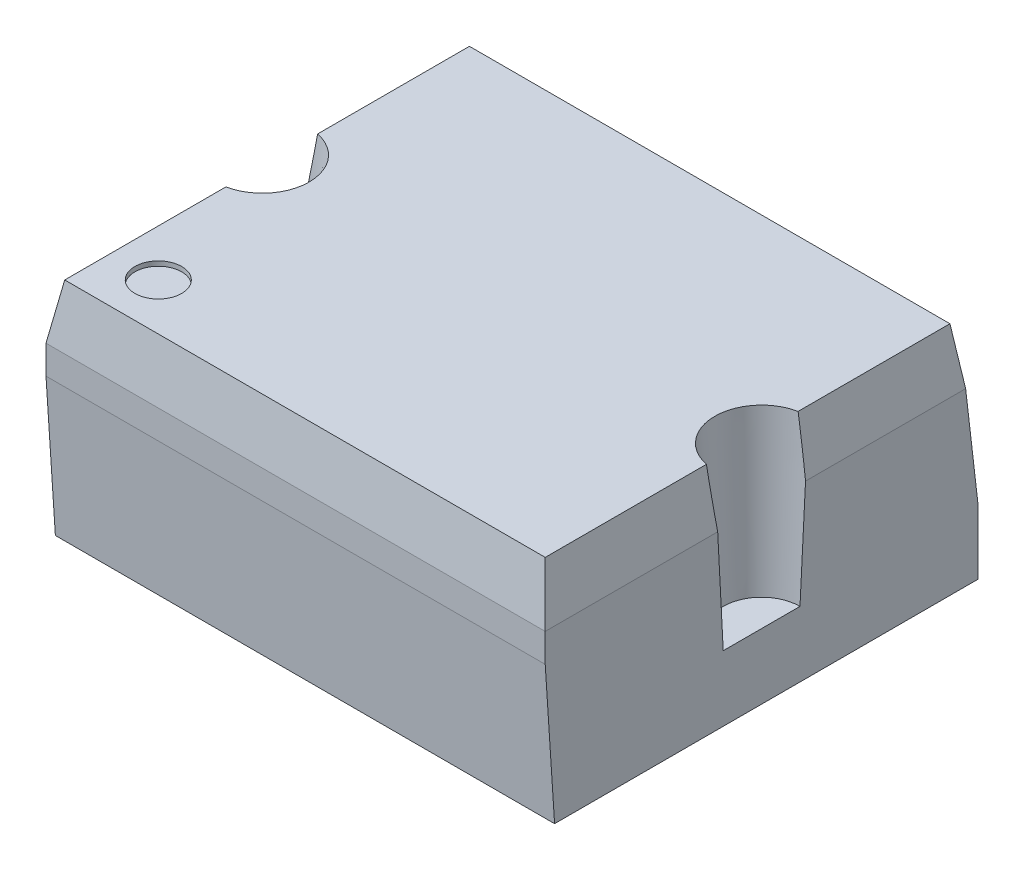
SolidWorks part; units mm, degrees
ref_plane "Front Plane" through (0, 0, 0) normal (0, 0, 1) x (1, 0, 0)
ref_plane "Top Plane" through (0, 0, 0) normal (0, 1, 0) x (1, 0, 0)
ref_plane "Right Plane" through (0, 0, 0) normal (1, 0, 0) x (0, 0, -1)
sketch "Sketch1" plane through (0, 0, 0) normal (0, 1, 0) x (1, 0, 0)
  line L1 (-5.335, -4.625) -> (5.335, -4.625)
  line L2 (-5.335, -4.625) -> (-5.335, 4.625)
  line L3 (-5.335, 4.625) -> (5.335, 4.625)
  line L4 (5.335, -4.625) -> (5.335, 4.625)
  line L5 (-5.335, -4.625) -> (5.335, 4.625) construction
  line L6 (-5.335, 4.625) -> (5.335, -4.625) construction
  point P0 (0, 0)
  dimension "D1" = 10.67
  dimension "D2" = 9.25
extrude "Boss-Extrude1" add sketch "Sketch1" along normal blind 4.83
sketch "Sketch3" plane through (5.335, 0, 0) normal (1, 0, 0) x (0, 0, -1)
  line L0 (4.625, 4.83) -> (4.225, 4.83)
  line L1 (-4.625, 4.83) -> (4.625, 4.83) construction
  line L2 (4.225, 4.83) -> (4.625, 1.39)
  line L3 (4.625, 4.83) -> (4.625, 0) construction
  line L4 (4.625, 1.39) -> (4.625, 4.83)
  dimension "D1" = 0.4
  dimension "D2" = 3.44
extrude "Cut-Extrude1" cut sketch "Sketch3" against normal through all
sketch "Sketch4" plane through (0, 0, 4.625) normal (0, 0, 1) x (1, 0, 0)
  line L0 (5.335, 4.83) -> (5.135, 4.83)
  line L1 (-5.335, 4.83) -> (5.335, 4.83) construction
  line L2 (5.135, 4.83) -> (5.335, 3.66)
  line L3 (5.335, 4.83) -> (5.335, 0) construction
  line L4 (5.335, 3.66) -> (5.335, 4.83)
  dimension "D1" = 0.2
  dimension "D2" = 1.17
extrude "Cut-Extrude2" cut sketch "Sketch4" against normal through all
mirror "Mirror1" about plane through (0, 0, 0) normal (1, 0, 0) of "Cut-Extrude2"
sketch "Sketch5" plane through (-5.335, 0, 0) normal (-1, 0, 0) x (0, 0, 1)
  line L0 (-4.225, 4.83) -> (4.625, 4.83) construction
  line L1 (4.625, 4.83) -> (4.625, 3.66) construction
  line L2 (4.425, 4.83) -> (4.625, 4.83)
  line L3 (4.625, 4.83) -> (4.625, 3.66)
  line L4 (4.425, 4.83) -> (4.625, 3.66)
  dimension "D1" = 0.2
extrude "Cut-Extrude3" cut sketch "Sketch5" against normal through all
sketch "Sketch6" plane through (-5.335, 0, 0) normal (-1, 0, 0) x (0, 0, 1)
  line L0 (4.625, 0) -> (4.625, 3.05)
  line L1 (4.625, 3.66) -> (4.625, 0) construction
  line L2 (4.625, 3.05) -> (4.425, 0)
  line L3 (-4.625, 0) -> (4.625, 0) construction
  line L4 (4.425, 0) -> (4.625, 0)
  dimension "D1" = 0.2
  dimension "D2" = 3.05
extrude "Cut-Extrude4" cut sketch "Sketch6" against normal through all
sketch "Sketch7" plane through (0, 4.83, 0) normal (0, 1, 0) x (1, 0, 0)
  line L0 (-5.335, 4.361) -> (-5.335, -4.625) construction
  line L1 (-5.335, 4.361) -> (-5.335, -4.625) construction
  line L2 (-2.6565, 0) -> (2.6565, 0) construction
  circle A0 centre (-5.335, 0) radius 1
  dimension "D1" = 2
extrude "Cut-Extrude5" cut sketch "Sketch7" against normal blind 3.43 draft 3
mirror "Mirror2" about plane through (0, 0, 0) normal (1, 0, 0) of "Cut-Extrude5"
sketch "Sketch8" plane through (0, 4.83, 0) normal (0, 1, 0) x (1, 0, 0)
  line L0 (5.135, -4.425) -> (-5.135, -4.425) construction
  line L1 (-5.135, -0.9798) -> (-5.135, -4.425) construction
  circle A0 centre (-4.135, -3.425) radius 0.5
  dimension "D3" = 1
  dimension "D1" = 1
  dimension "D2" = 1
extrude "Cut-Extrude6" cut sketch "Sketch8" against normal blind 0.1
